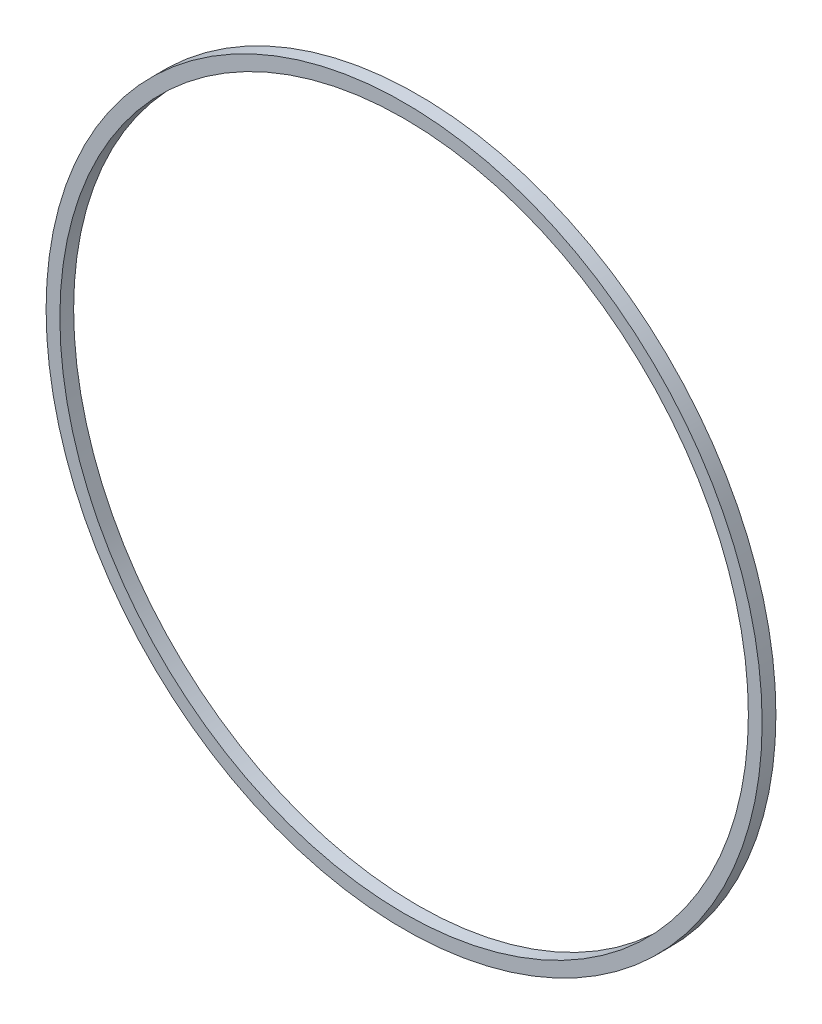
SolidWorks part; units mm, degrees
ref_plane "Front Plane" through (0, 0, 0) normal (0, 0, 1) x (1, 0, 0)
ref_plane "Top Plane" through (0, 0, 0) normal (0, 1, 0) x (1, 0, 0)
ref_plane "Right Plane" through (0, 0, 0) normal (1, 0, 0) x (0, 0, -1)
sketch "Sketch1" plane through (0, 0, 0) normal (0, 0, 1) x (1, 0, 0)
  circle A0 centre (-19.8706, -20.9032) radius 50
  circle A1 centre (-19.8706, -20.9032) radius 52
  dimension "D8" = 10
extrude "Boss-Extrude5" add sketch "Sketch1" along normal blind 2
